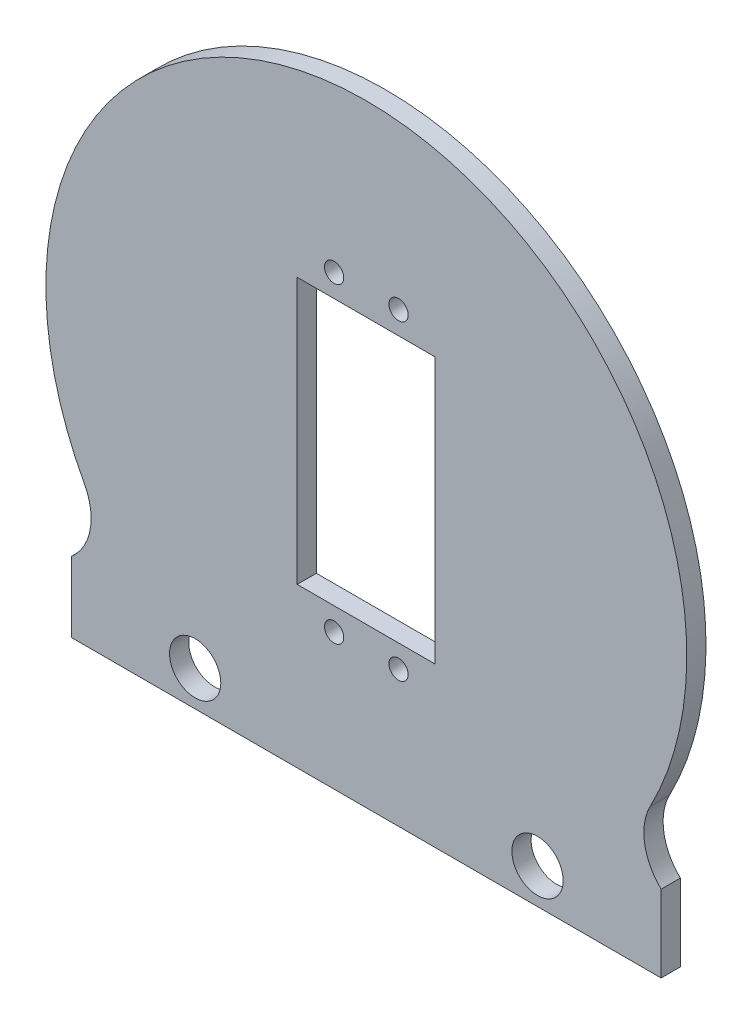
SolidWorks part; units mm, degrees
material "Beech"
ref_plane "Front Plane" through (0, 0, 0) normal (0, 0, 1) x (1, 0, 0)
ref_plane "Top Plane" through (0, 0, 0) normal (0, 1, 0) x (1, 0, 0)
ref_plane "Right Plane" through (0, 0, 0) normal (1, 0, 0) x (0, 0, -1)
sketch "Sketch1" plane through (0, 0, 0) normal (0, 0, 1) x (1, 0, 0)
  line L0 (-26.71, -53.5144) -> (-26.71, 55.4652) construction
  line L1 (-10.7948, 20.75) -> (10.7052, 20.75)
  line L2 (-46, -34.5466) -> (-46, -45.541)
  line L3 (-46, -45.541) -> (46, -45.541)
  line L4 (46, -33.541) -> (46, -45.541)
  line L5 (-10.7948, 20.75) -> (-10.7948, -20.75)
  line L6 (-10.7948, -20.75) -> (10.7052, -20.75)
  line L7 (10.7052, 20.75) -> (10.7052, -20.75)
  line L8 (78.6066, 0) -> (-100.1963, 0) construction
  line L9 (0, -70.3617) -> (0, 70.3617) construction
  line L10 (-157.3149, -40.0438) -> (65.3149, -40.0438) construction
  arc A0 (44.2977, -23.1886) -> (-43.9901, -23.7669) centre (0, 0) ccw
  arc A1 (44.2977, -23.1886) -> (46, -33.541) centre (52.0257, -27.234) ccw
  circle A2 centre (-26.71, -40.0438) radius 4
  arc A3 (-43.9901, -23.7669) -> (-46, -34.5466) centre (-51.6645, -27.9132) cw
  circle A4 centre (26.71, -40.0438) radius 4
  circle A5 centre (5.025, -24.3) radius 1.5
  circle A6 centre (-5.025, -24.3) radius 1.5
  circle A7 centre (5.025, 24.3) radius 1.5
  circle A8 centre (-5.025, 24.3) radius 1.5
  point P3 (0, -30)
  point P6 (0, -45.541)
  point P10 (0, 0)
  point P25 (0, 0)
  point P26 (-10.7948, 0)
  point P34 (-10.7948, 0)
  point P37 (0, 0)
  point P40 (-46, -40.0438)
  dimension "D2" = 3.55
  dimension "D5" = 3
  dimension "D9" = 3.55
  dimension "D11" = 108.9796
  dimension "D12" = 19.29
  dimension "D13" = 70.3617
  dimension "D14" = 140.7233
  dimension "D10" = 8.7228
  dimension "D8" = 50
  dimension "D7" = 8.7228
  dimension "D15" = 8
  dimension "D17" = 46
  dimension "D3" = 20.75
  dimension "D4" = 92
  dimension "D6" = 21.5
  dimension "D16" = 222.6298
extrude "Boss-Extrude1" add sketch "Sketch1" along normal blind 3
